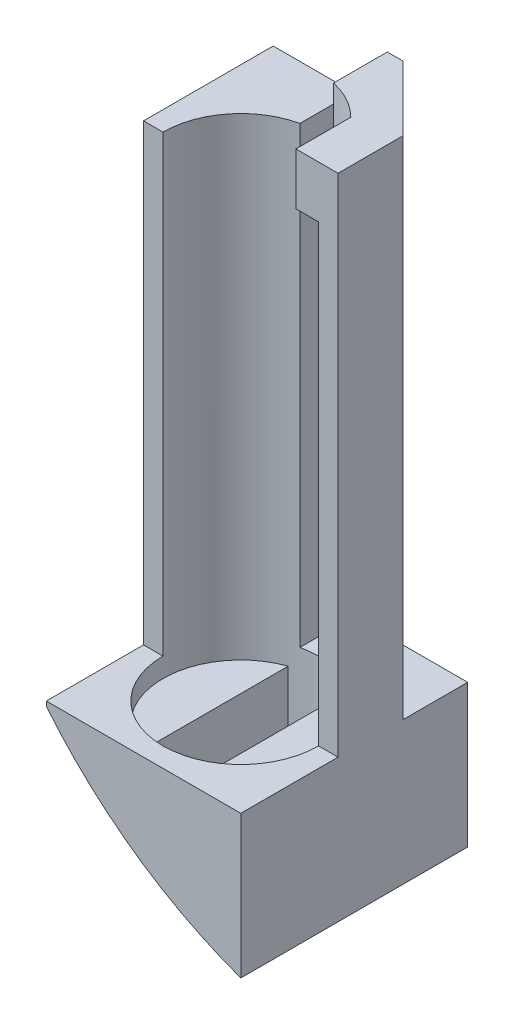
SolidWorks part; units mm, degrees
ref_plane "Front Plane" through (0, 0, 0) normal (1, 0, 0) x (0, 1, 0)
ref_plane "Top Plane" through (0, 0, 0) normal (0, 0, 1) x (0, 1, 0)
ref_plane "Right Plane" through (0, 0, 0) normal (0, 1, 0) x (-1, 0, 0)
sketch "Sketch1" plane through (0, 0, 0) normal (0, 1, 0) x (-1, 0, 0)
  line L0 (-12, 0) -> (-15, 0)
  line L1 (-15, 0) -> (-15, -10)
  line L2 (-15, -10) -> (-5, -20)
  line L3 (-5, -20) -> (15, -20)
  line L4 (15, -20) -> (15, 0)
  line L5 (15, 0) -> (12, 0)
  line L6 (-2.6, -11.7149) -> (-2.6, -17.2)
  line L7 (-2.6, -17.2) -> (2.6, -17.2)
  line L8 (2.6, -17.2) -> (2.6, -11.7149)
  line L9 (0, -17.2) -> (0, 0) construction
  arc A0 (-12, 0) -> (-2.6, -11.7149) centre (0, 0) ccw
  arc A1 (2.6, -11.7149) -> (12, 0) centre (0, 0) ccw
  point P16 (0, -17.2)
  dimension "D1" = 24
  dimension "D2" = 30
  dimension "D3" = 10
  dimension "D4" = 10
  dimension "D5" = 20
  dimension "D6" = 5.2
  dimension "D7" = 17.2
extrude "Boss-Extrude1" add sketch "Sketch1" along normal blind 70
sketch "Sketch5" plane through (0, 0, 0) normal (0, 1, 0) x (-1, 0, 0)
  line L1 (-15, -20) -> (15, -20)
  line L2 (-15, -20) -> (-15, 15)
  line L3 (-15, 15) -> (15, 15)
  line L4 (15, -20) -> (15, 15)
  point P5 (15, -20)
  dimension "D1" = 15
  dimension "D2" = 30
extrude "Boss-Extrude3" add sketch "Sketch5" against normal blind 22
sketch "Sketch6" plane through (0, 0, 0) normal (0, 0, 1) x (0, 1, 0)
  line L0 (-22, -15) -> (0, -15) construction
  line L2 (42.8749, -38.5) -> (42.8749, -15) construction
  line L3 (70, -15) -> (0, -15) construction
  circle A0 centre (42.8749, -38.5) radius 69
  circle A1 centre (42.8749, -38.5) radius 108.0355
  dimension "D1" = 138
  dimension "D2" = 23.5
extrude "Cut-Extrude1" cut sketch "Sketch6" against normal through all and the other way through all
sketch "Sketch7" plane through (0, 0, 0) normal (0, 1, 0) x (-1, 0, 0)
  circle A0 centre (0, 0) radius 12
extrude "Cut-Extrude2" cut sketch "Sketch7" against normal blind 3
sketch "Sketch8" plane through (0, 0, 0) normal (0, 1, 0) x (-1, 0, 0)
  line L0 (-4, 11.3137) -> (-4, -11.3137)
  line L1 (4, -11.3137) -> (4, 11.3137)
  arc A0 (-4, -11.3137) -> (4, -11.3137) centre (0, 0) ccw
  arc A1 (4, 11.3137) -> (-4, 11.3137) centre (0, 0) ccw
  dimension "D2" = 24
  dimension "D1" = 4
extrude "Cut-Extrude3" cut sketch "Sketch8" against normal through all
sketch "Sketch10" plane through (0, 70, 0) normal (0, 1, 0) x (-1, 0, 0)
  line L0 (-15, -10) -> (-5, -20)
  line L1 (-15, 0) -> (-8.5, 0)
  line L2 (-15, 0) -> (-15, -10)
  line L4 (-8.5, 0) -> (-8.5, -8.4705)
  line L5 (-2.6, -20) -> (-2.6, -11.7149)
  line L6 (-5, -20) -> (-2.6, -20)
  arc A0 (-4, 11.3137) -> (-4, -11.3137) centre (0, 0) ccw construction
  arc A1 (-8.5, -8.4705) -> (-2.6, -11.7149) centre (0, 0) ccw
  dimension "D1" = 6.5
extrude "Boss-Extrude4" add sketch "Sketch10" along normal blind 8
